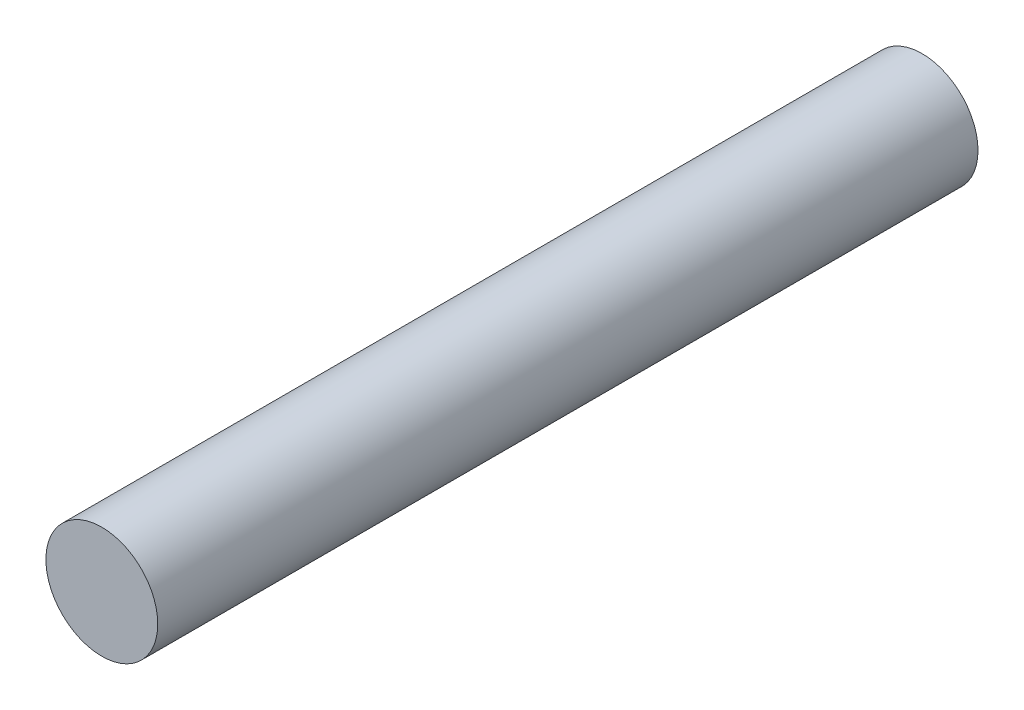
SolidWorks part; units mm, degrees
ref_plane "Front Plane" through (0, 0, 0) normal (0, 0, 1) x (1, 0, 0)
ref_plane "Top Plane" through (0, 0, 0) normal (0, 1, 0) x (1, 0, 0)
ref_plane "Right Plane" through (0, 0, 0) normal (1, 0, 0) x (0, 0, -1)
sketch "Sketch1" plane through (0, 0, 0) normal (0, 0, 1) x (1, 0, 0)
  circle A0 centre (0, 0) radius 3.75
  dimension "D1" = 7.5
extrude "Boss-Extrude1" add sketch "Sketch1" along normal mid plane 55
equation "\"D1@Boss-Extrude1\"=50+5"
